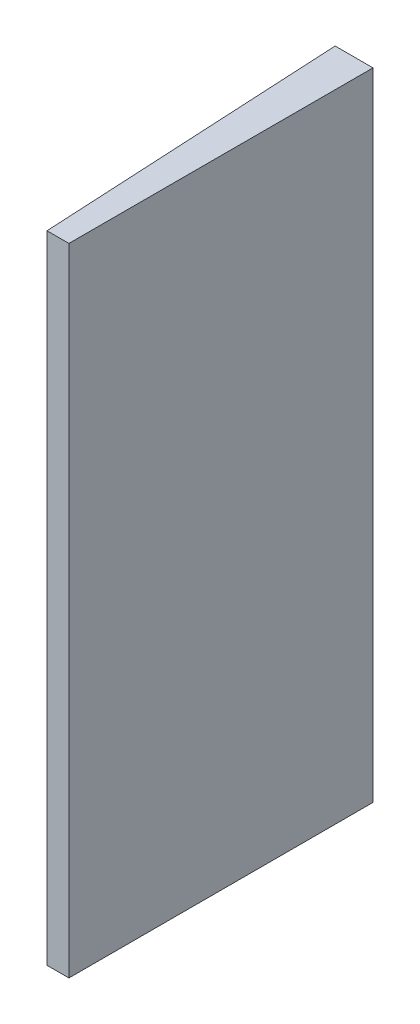
SolidWorks part; units mm, degrees
ref_plane "Top Plane" through (0, 0, 0) normal (0, 0, 1) x (1, 0, 0)
ref_plane "Front Plane" through (0, 0, 0) normal (0, 1, 0) x (1, 0, 0)
ref_plane "Right Plane" through (0, 0, 0) normal (1, 0, 0) x (0, 0, -1)
sketch "Sketch1" plane through (0, 0, 0) normal (0, 1, 0) x (1, 0, 0)
  line L12 (0, 20.075) -> (0, -20.075)
  line L13 (0, 20.075) -> (-5, 20.075)
  line L14 (-5, 20.075) -> (-2.8958, -20.075)
  line L15 (-2.8958, -20.075) -> (0, -20.075)
  dimension "D1" = 40.15
  dimension "D2" = 5
  dimension "D3" = 93
  dimension "D4" = 20.075
extrude "Boss-Extrude1" add sketch "Sketch1" along normal mid plane 84
sketch "Sketch2" plane through (-3.9371, 0, 0.2063) normal (-0.9986, 0, 0.0523) x (0.0523, 0, 0.9986)
  circle A0 centre (-5.1092, -29.8957) radius 3.3 construction
  circle A1 centre (-5.1092, 29.8957) radius 3.3 construction
  circle A2 centre (-5.1092, -29.8957) radius 3.3
  circle A3 centre (-5.1092, 29.8957) radius 3.3
extrude "Boss-Extrude2" add sketch "Sketch2" along normal blind 1.8
